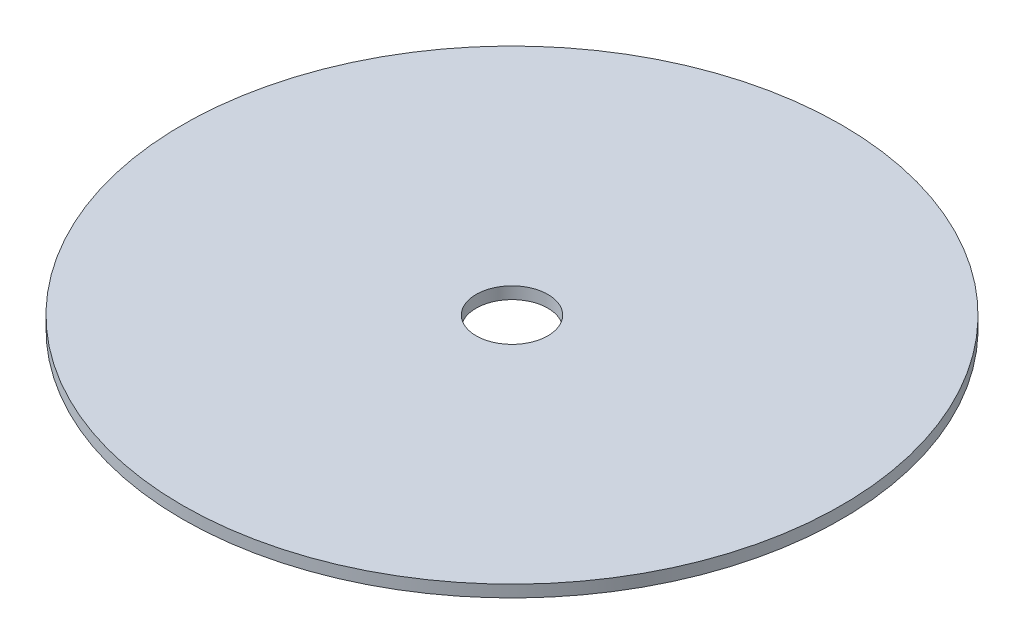
SolidWorks part; units mm, degrees
ref_plane "Спереди" through (0, 0, 0) normal (0, 0, 1) x (1, 0, 0)
ref_plane "Сверху" through (0, 0, 0) normal (0, 1, 0) x (1, 0, 0)
ref_plane "Справа" through (0, 0, 0) normal (1, 0, 0) x (0, 0, -1)
other "Configuration Table"
sketch "Sketch1" plane through (0, 0, 0) normal (0, 1, 0) x (1, 0, 0)
  circle A0 centre (0, 0) radius 24.8
  circle A1 centre (0, 0) radius 2.7
extrude "Boss-Extrude1" add sketch "Sketch1" along normal blind 0.9
sketch "Sketch2" plane through (0, 0, 0) normal (0, -1, 0) x (1, 0, 0)
  circle A0 centre (0, 0) radius 21.2
  circle A1 centre (0, 0) radius 10.15
extrude "Boss-Extrude2" add sketch "Sketch2" along normal blind 2.25
